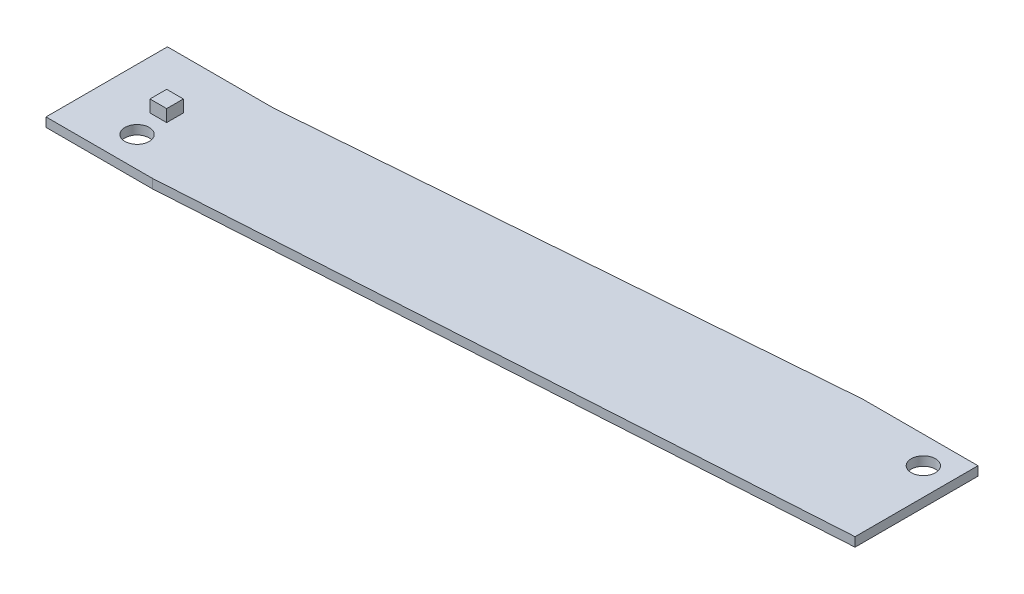
SolidWorks part; units mm, degrees
ref_plane "Front Plane" through (0, 0, 0) normal (0, 0, 1) x (1, 0, 0)
ref_plane "Top Plane" through (0, 0, 0) normal (0, 1, 0) x (1, 0, 0)
ref_plane "Right Plane" through (0, 0, 0) normal (1, 0, 0) x (0, 0, -1)
sketch "Sketch1" plane through (0, 0, 0) normal (0, 1, 0) x (1, 0, 0)
  line L0 (87.2, 5.6) -> (72, 5.6)
  line L5 (87.2, 5.6) -> (87.2, -10.6)
  line L6 (0, 0) -> (72, 5.6)
  line L7 (87.2, -10.6) -> (0, -16)
  line L8 (0, 0) -> (-14, 0)
  line L9 (0, -16) -> (-14, -16)
  line L10 (-14, 0) -> (-14, -16)
  point P4 (0, 0)
  dimension "D2" = 0
  dimension "D3" = 15.2
  dimension "D4" = 16.2
  dimension "D5" = 16
  dimension "D6" = 14
  dimension "D7" = 14
  dimension "D8" = 87.2
  dimension "D9" = 0
extrude "Boss-Extrude1" add sketch "Sketch1" along normal blind 1.2
sketch "Sketch2" plane through (0, 1.2, 0) normal (0, 1, 0) x (1, 0, 0)
  line L2 (-14, -16) -> (0, -16) construction
  line L3 (87.2, -10.6) -> (87.2, 5.6) construction
  line L4 (87.2, 5.6) -> (72, 5.6) construction
  circle A0 centre (-6, -12) radius 1.6
  circle A1 centre (83.6, 2) radius 1.6
  dimension "D1" = 3.2
  dimension "D2" = 4
  dimension "D3" = 6
  dimension "D4" = 3.2
  dimension "D5" = 3.6
  dimension "D6" = 3.6
extrude "Cut-Extrude1" cut sketch "Sketch2" against normal up to surface (1.2 mm away) up to face at (31.2, 0, 4.4857)
sketch "Sketch3" plane through (0, 1.2, 0) normal (0, 1, 0) x (1, 0, 0)
  line L1 (-7.6, -6.5) -> (-5.4, -6.5)
  line L2 (-7.6, -6.5) -> (-7.6, -8.7)
  line L3 (-7.6, -8.7) -> (-5.4, -8.7)
  line L4 (-5.4, -6.5) -> (-5.4, -8.7)
  circle A0 centre (-6, -12) radius 1.6 construction
  dimension "D1" = 1.6
  dimension "D2" = 3.3
  dimension "D3" = 2.2
  dimension "D4" = 2.2
extrude "Boss-Extrude2" add sketch "Sketch3" along normal blind 1.6
